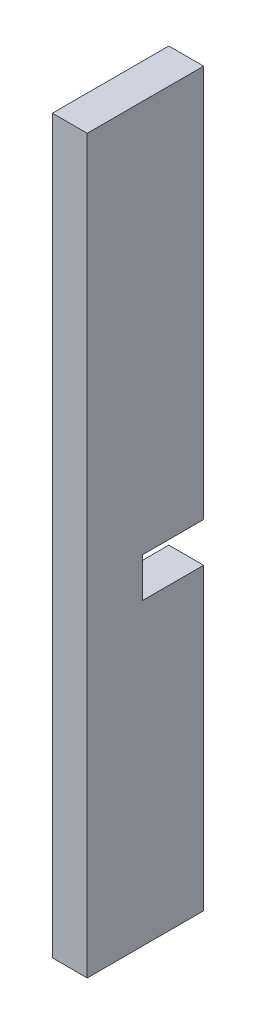
SolidWorks part; units mm, degrees
material "Chêne"
ref_plane "Plan de face" through (0, 0, 0) normal (0, 0, 1) x (1, 0, 0)
ref_plane "Plan de dessus" through (0, 0, 0) normal (0, 1, 0) x (1, 0, 0)
ref_plane "Plan de droite" through (0, 0, 0) normal (1, 0, 0) x (0, 0, -1)
sketch "Esquisse1" plane through (0, 0, 0) normal (0, 0, 1) x (1, 0, 0)
  line L1 (11, 231) -> (-11, 231)
  line L2 (11, 231) -> (11, -231)
  line L3 (11, -231) -> (-11, -231)
  line L4 (-11, 231) -> (-11, -231)
  point P4 (0, 231)
  point P5 (11, 0)
  point P10 (1151.7427, -217.5423)
  dimension "D1" = 22
  dimension "D2" = 462
extrude "Boss.-Extru.1" add sketch "Esquisse1" along normal blind 73.5
sketch "Esquisse2" plane through (-11, 0, 0) normal (-1, 0, 0) x (0, 0, 1)
  line L0 (73.5, 231) -> (0, 231) construction
  line L4 (0, -17) -> (38.5, -17)
  line L5 (0, -42) -> (0, -17)
  line L6 (38.5, -42) -> (0, -42)
  line L7 (38.5, -17) -> (38.5, -42)
  line L11 (0, 231) -> (0, -231) construction
  point P14 (-481.4129, -80.8583)
  dimension "D1" = 38.5
  dimension "D2" = 25
  dimension "D3" = 248
extrude "Enlèv. mat.-Extru.1" cut sketch "Esquisse2" against normal blind 35
